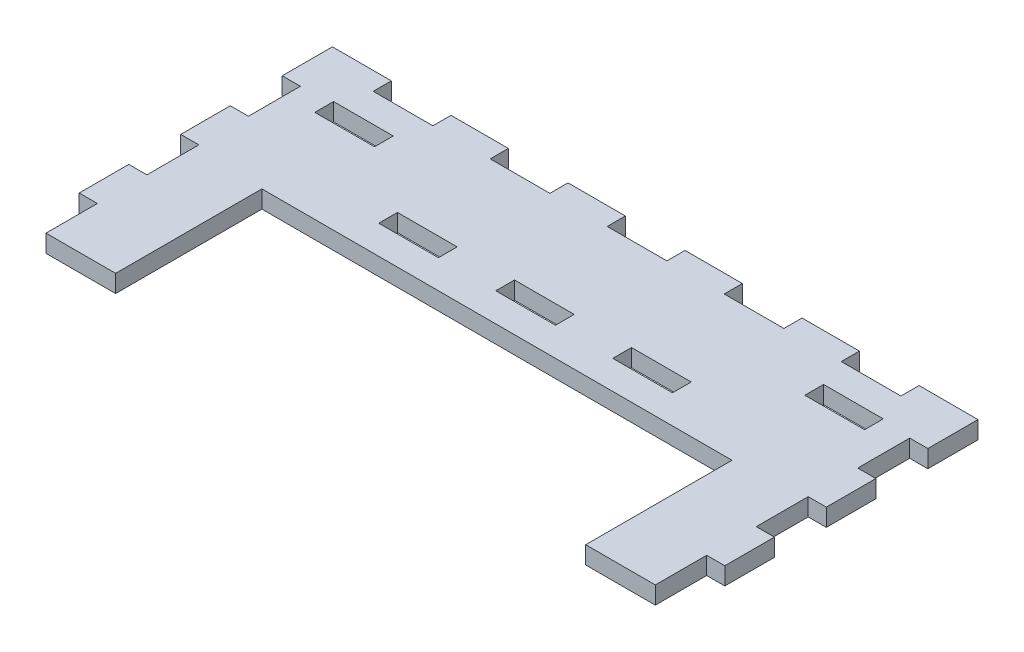
SolidWorks part; units mm, degrees
ref_plane "Front Plane" through (0, 0, 0) normal (0, 0, 1) x (1, 0, 0)
ref_plane "Top Plane" through (0, 0, 0) normal (0, 1, 0) x (1, 0, 0)
ref_plane "Right Plane" through (0, 0, 0) normal (1, 0, 0) x (0, 0, -1)
sketch "Sketch1" plane through (0, 0, 0) normal (0, 1, 0) x (1, 0, 0)
  line L0 (0, 0) -> (0, 52.05) construction
  line L1 (-55.1722, 52.05) -> (55.1722, 52.05)
  line L2 (-55.1722, 52.05) -> (-55.1722, 0)
  line L3 (-55.1722, 0) -> (55.1722, 0) construction
  line L4 (55.1722, 52.05) -> (55.1722, 0)
  line L6 (40.1722, 0) -> (40.1722, 25)
  line L7 (40.1722, 25) -> (-40.1722, 25)
  line L8 (-40.1722, 25) -> (-40.1722, 0)
  line L9 (55.1722, 0) -> (40.1722, 0)
  line L10 (-40.1722, 0) -> (-55.1722, 0)
  dimension "D1" = 15
sketch "Sketch2" plane through (0, 0, 0) normal (1, 0, 0) x (0, 0, -1)
  line L1 (0, 0) -> (52.05, 0)
  line L2 (0, 0) -> (0, 3)
  line L3 (0, 3) -> (52.05, 3)
  line L4 (52.05, 0) -> (52.05, 3)
extrude "Boss-Extrude1" add sketch "Sketch1" along normal up to vertex (3 mm away) up to point (0, 3, -52.05)
sketch "Sketch3" plane through (0, 0, 0) normal (0, 1, 0) x (1, 0, 0)
  line L0 (55.1722, 52.05) -> (55.1722, 0) construction
  line L1 (55.1722, 0) -> (40.1722, 0) construction
  line L2 (40.1722, 0) -> (40.1722, 25) construction
  line L3 (40.1722, 25) -> (-40.1722, 25) construction
  line L4 (-40.1722, 25) -> (-40.1722, 0) construction
  line L5 (-40.1722, 0) -> (-55.1722, 0) construction
  line L6 (-55.1722, 52.05) -> (-55.1722, 0) construction
  line L7 (-55.1722, 52.05) -> (55.1722, 52.05) construction
  line L8 (55.1722, 52.05) -> (55.1722, 0) construction
  line L9 (55.1722, 0) -> (40.1722, 0) construction
  line L10 (40.1722, 0) -> (40.1722, 25) construction
  line L11 (40.1722, 25) -> (-40.1722, 25) construction
  line L12 (-40.1722, 25) -> (-40.1722, 0) construction
  line L13 (-40.1722, 0) -> (-55.1722, 0) construction
  line L14 (-55.1722, 52.05) -> (-55.1722, 0) construction
  line L15 (-55.1722, 52.05) -> (55.1722, 52.05) construction
  line L16 (36.8722, 52.05) -> (36.8722, 25) construction
  line L17 (-36.8722, 52.05) -> (-36.8722, 25) construction
  line L18 (55.1722, 49.05) -> (-55.1722, 49.05) construction
  line L19 (55.1722, 40.95) -> (-55.1722, 40.95) construction
  line L20 (55.1722, 43.95) -> (-55.1722, 43.95) construction
  line L21 (-55.1722, 33) -> (55.1722, 33) construction
  line L22 (52.1722, 52.05) -> (52.1722, 0) construction
  line L23 (-52.1722, 52.05) -> (-52.1722, 0) construction
  line L24 (0, 52.05) -> (0, 0) construction
  line L25 (46.8722, 52.05) -> (46.8722, 49.05) construction
  line L26 (46.8722, 43.95) -> (46.8722, 40.95) construction
  line L27 (40.1722, 25) -> (55.1722, 25) construction
  line L28 (-40.1722, 25) -> (-55.1722, 25) construction
  line L30 (35, 33) -> (35, 30) construction
  line L31 (36.8722, 30) -> (-36.8722, 30) construction
  line L32 (-5, 52.05) -> (-5, 49.05) construction
  line L33 (25, 33) -> (25, 30) construction
  line L34 (25, 31.5) -> (35, 31.5) construction
  line L35 (5, 33) -> (5, 30) construction
  line L36 (5, 31.5) -> (-5, 31.5) construction
  line L37 (25, 31.5) -> (15, 31.5) construction
  line L38 (15, 31.5) -> (5, 31.5) construction
  line L39 (15, 33) -> (15, 30) construction
  line L40 (5, 52.05) -> (5, 49.05) construction
  line L41 (15, 52.05) -> (15, 49.05) construction
  line L42 (25, 52.05) -> (25, 49.05) construction
  line L43 (52.1722, 43.375) -> (55.1722, 43.375) construction
  line L44 (55.1722, 34.7) -> (52.1722, 34.7) construction
  line L45 (53.6722, 34.7) -> (53.6722, 43.375) construction
  line L46 (53.6722, 43.375) -> (53.6722, 52.05) construction
  line L47 (53.6722, 34.7) -> (53.6722, 26.025) construction
  line L48 (55.1722, 26.025) -> (52.1722, 26.025) construction
  line L49 (55.1722, 17.35) -> (52.1722, 17.35) construction
  line L50 (53.6722, 26.025) -> (53.6722, 17.35) construction
  line L51 (55.1722, 8.675) -> (52.1722, 8.675) construction
  line L52 (53.6722, 17.35) -> (53.6722, 8.675) construction
  line L53 (53.6722, 8.675) -> (53.6722, 0) construction
  line L54 (35, 52.05) -> (35, 49.05) construction
  line L55 (45, 49.05) -> (45, 52.05) construction
  line L56 (35, 50.55) -> (45, 50.55) construction
  line L57 (35, 50.55) -> (25, 50.55) construction
  dimension "D1" = 10
  dimension "D2" = 8.675
  dimension "D3" = 10
sketch "Sketch4" plane through (0, 0, 0) normal (0, 1, 0) x (1, 0, 0)
  line L0 (0, 0) -> (0, 52.05) construction
  line L1 (45.1, 52.15) -> (34.9, 52.15)
  line L2 (45.1, 52.15) -> (45.1, 48.95)
  line L3 (45.1, 48.95) -> (34.9, 48.95)
  line L4 (34.9, 52.15) -> (34.9, 48.95)
  line L5 (46.9722, 44.05) -> (36.7722, 44.05)
  line L6 (46.9722, 44.05) -> (46.9722, 40.85)
  line L7 (46.9722, 40.85) -> (36.7722, 40.85)
  line L8 (36.7722, 44.05) -> (36.7722, 40.85)
  line L9 (55.2722, 43.475) -> (52.0722, 43.475)
  line L10 (55.2722, 43.475) -> (55.2722, 34.6)
  line L11 (55.2722, 34.6) -> (52.0722, 34.6)
  line L12 (52.0722, 43.475) -> (52.0722, 34.6)
  line L13 (55.2722, 26.125) -> (52.0722, 26.125)
  line L14 (55.2722, 26.125) -> (55.2722, 17.25)
  line L15 (55.2722, 17.25) -> (52.0722, 17.25)
  line L16 (52.0722, 26.125) -> (52.0722, 17.25)
  line L17 (55.2722, 8.775) -> (52.0722, 8.775)
  line L18 (55.2722, 8.775) -> (55.2722, -0.1)
  line L19 (55.2722, -0.1) -> (52.0722, -0.1)
  line L20 (52.0722, 8.775) -> (52.0722, -0.1)
  line L21 (20, 33.1) -> (20, 33) construction
  line L22 (20, 29.9) -> (20, 30) construction
  line L24 (-55.1722, 33) -> (55.1722, 33) construction
  line L25 (25.1, 33.1) -> (14.9, 33.1)
  line L26 (25.1, 33.1) -> (25.1, 29.9)
  line L27 (25.1, 29.9) -> (14.9, 29.9)
  line L28 (14.9, 33.1) -> (14.9, 29.9)
  line L29 (5.1, 33.1) -> (-5.1, 33.1)
  line L30 (5.1, 33.1) -> (5.1, 29.9)
  line L31 (5.1, 29.9) -> (-5.1, 29.9)
  line L32 (-5.1, 33.1) -> (-5.1, 29.9)
  line L33 (0, 0) -> (0, 52.05) construction
  line L34 (40, 52.15) -> (40, 52.05) construction
  line L35 (40, 48.95) -> (40, 49.05) construction
  line L36 (34.9, 50.55) -> (35, 50.55) construction
  line L37 (45.1, 50.55) -> (45, 50.55) construction
  line L39 (-55.1722, 52.05) -> (55.1722, 52.05) construction
  line L40 (55.1722, 49.05) -> (-55.1722, 49.05) construction
  line L42 (52.0722, 39.0375) -> (52.1722, 39.0375) construction
  line L43 (55.2722, 39.0375) -> (55.1722, 39.0375) construction
  line L44 (53.6722, 43.475) -> (53.6722, 43.375) construction
  line L45 (53.6722, 34.6) -> (53.6722, 34.7) construction
  line L46 (53.6722, 26.125) -> (53.6722, 26.025) construction
  line L47 (53.6722, 17.25) -> (53.6722, 17.35) construction
  line L48 (53.6722, 8.775) -> (53.6722, 8.675) construction
  line L49 (53.6722, -0.1) -> (53.6722, 0) construction
  line L50 (41.8722, 44.05) -> (41.8722, 43.95) construction
  line L51 (41.8722, 40.85) -> (41.8722, 40.95) construction
  line L52 (55.1722, 43.95) -> (-55.1722, 43.95) construction
  line L53 (55.1722, 40.95) -> (-55.1722, 40.95) construction
  line L54 (52.1722, 43.375) -> (55.1722, 43.375) construction
  line L55 (55.1722, 34.7) -> (52.1722, 34.7) construction
  line L56 (52.1722, 52.05) -> (52.1722, 0) construction
  line L57 (55.1722, 52.05) -> (55.1722, 0) construction
  line L58 (55.1722, 26.025) -> (52.1722, 26.025) construction
  line L59 (55.1722, 17.35) -> (52.1722, 17.35) construction
  line L60 (55.1722, 0) -> (40.1722, 0) construction
  line L61 (55.1722, 8.675) -> (52.1722, 8.675) construction
  line L62 (36.8722, 30) -> (-36.8722, 30) construction
  line L63 (35, 52.05) -> (35, 49.05) construction
  line L64 (36.8722, 42.45) -> (36.7722, 42.45) construction
  line L65 (36.8722, 52.05) -> (36.8722, 25) construction
  line L66 (46.9722, 42.45) -> (46.8722, 42.45) construction
  line L67 (46.8722, 43.95) -> (46.8722, 40.95) construction
  line L69 (25.1, 52.15) -> (14.9, 52.15)
  line L70 (25.1, 31.5) -> (25, 31.5) construction
  line L71 (14.9, 31.5) -> (15, 31.5) construction
  line L72 (5.1, 31.5) -> (5, 31.5) construction
  line L73 (5, 33) -> (5, 30) construction
  line L74 (15, 33) -> (15, 30) construction
  line L75 (25, 33) -> (25, 30) construction
  line L76 (-55.2722, 8.775) -> (-52.0722, 8.775)
  line L77 (-55.2722, 8.775) -> (-55.2722, -0.1)
  line L78 (-55.2722, -0.1) -> (-52.0722, -0.1)
  line L79 (-52.0722, 8.775) -> (-52.0722, -0.1)
  line L80 (-55.2722, 26.125) -> (-52.0722, 26.125)
  line L81 (-55.2722, 26.125) -> (-55.2722, 17.25)
  line L82 (-55.2722, 17.25) -> (-52.0722, 17.25)
  line L83 (-52.0722, 26.125) -> (-52.0722, 17.25)
  line L84 (-55.2722, 43.475) -> (-52.0722, 43.475)
  line L85 (-55.2722, 43.475) -> (-55.2722, 34.6)
  line L86 (-55.2722, 34.6) -> (-52.0722, 34.6)
  line L87 (-52.0722, 43.475) -> (-52.0722, 34.6)
  line L88 (-45.1, 52.15) -> (-45.1, 48.95)
  line L89 (-45.1, 52.15) -> (-34.9, 52.15)
  line L90 (-34.9, 52.15) -> (-34.9, 48.95)
  line L91 (-45.1, 48.95) -> (-34.9, 48.95)
  line L92 (-46.9722, 44.05) -> (-46.9722, 40.85)
  line L93 (-46.9722, 40.85) -> (-36.7722, 40.85)
  line L94 (-36.7722, 44.05) -> (-36.7722, 40.85)
  line L95 (-46.9722, 44.05) -> (-36.7722, 44.05)
  line L96 (25.1, 52.15) -> (25.1, 48.95)
  line L97 (25.1, 48.95) -> (14.9, 48.95)
  line L98 (14.9, 52.15) -> (14.9, 48.95)
  line L99 (5.1, 52.15) -> (-5.1, 52.15)
  line L100 (-25.1, 33.1) -> (-25.1, 29.9)
  line L101 (-25.1, 29.9) -> (-14.9, 29.9)
  line L102 (-14.9, 33.1) -> (-14.9, 29.9)
  line L103 (-25.1, 33.1) -> (-14.9, 33.1)
  line L104 (5.1, 52.15) -> (5.1, 48.95)
  line L105 (5.1, 48.95) -> (-5.1, 48.95)
  line L106 (-5.1, 52.15) -> (-5.1, 48.95)
  line L107 (-14.9, 52.15) -> (-25.1, 52.15)
  line L108 (-14.9, 52.15) -> (-14.9, 48.95)
  line L109 (-14.9, 48.95) -> (-25.1, 48.95)
  line L110 (-25.1, 52.15) -> (-25.1, 48.95)
  dimension "D1" = 0.1
extrude "Cut-Extrude1" cut sketch "Sketch4" along normal through all
